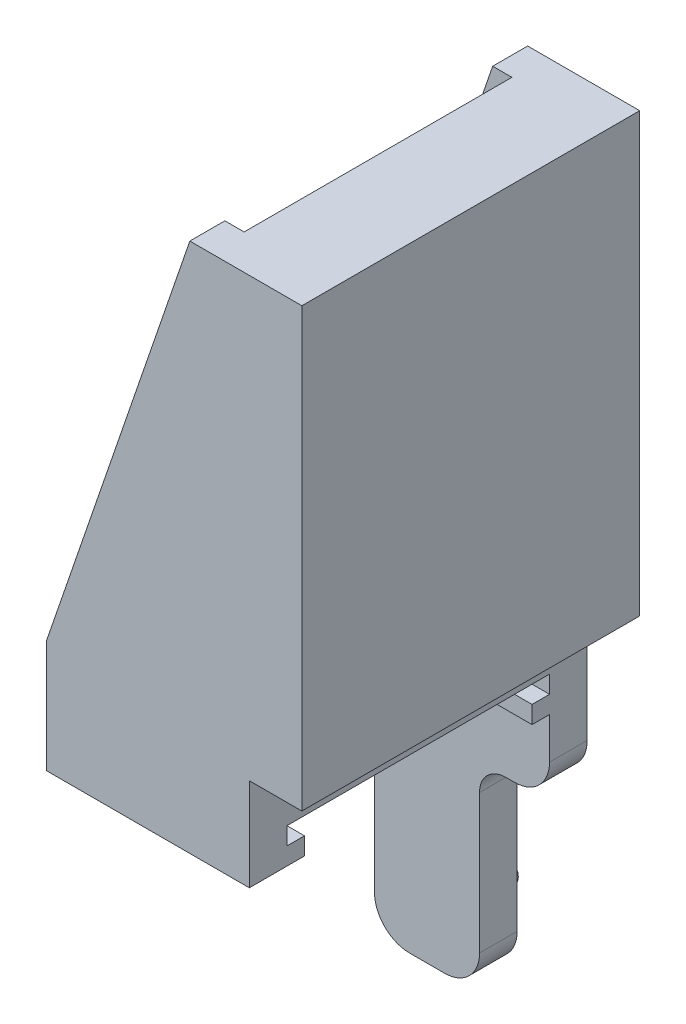
SolidWorks part; units mm, degrees
ref_plane "Alzado" through (0, 0, 0) normal (0, 0, 1) x (1, 0, 0)
ref_plane "Planta" through (0, 0, 0) normal (0, 1, 0) x (1, 0, 0)
ref_plane "Vista lateral" through (0, 0, 0) normal (1, 0, 0) x (0, 0, -1)
sketch "Croquis1" plane through (0, 0, 0) normal (0, 0, 1) x (1, 0, 0)
  line L0 (5.8, 23.05) -> (2.4, 23.05)
  line L2 (2.4, 23.05) -> (-5.8, -0.85)
  line L9 (1.8, -13.107) -> (1.8, -21.05)
  line L10 (-0.2, -23.05) -> (-2.2, -23.05)
  line L11 (-4.2, -21.05) -> (-4.2, -12.1093)
  line L12 (-4.7023, -11.6093) -> (-4.7953, -11.6097)
  line L13 (-5.8, -10.6097) -> (-5.8, -0.85)
  line L14 (3.3, -11.607) -> (3.8, -11.607)
  line L15 (5.8, -9.607) -> (5.8, 23.05)
  arc A0 (3.8, -11.607) -> (5.8, -9.607) centre (3.8, -9.607) ccw
  arc A1 (1.8, -13.107) -> (3.3, -11.607) centre (3.3, -13.107) cw
  arc A2 (1.8, -21.05) -> (-0.2, -23.05) centre (-0.2, -21.05) cw
  arc A3 (-2.2, -23.05) -> (-4.2, -21.05) centre (-2.2, -21.05) cw
  arc A4 (-4.7953, -11.6097) -> (-5.8, -10.6097) centre (-4.8, -10.6097) cw
  arc A5 (-4.2, -12.1093) -> (-4.7023, -11.6093) centre (-4.7, -12.1093) ccw
  point P0 (0, 0)
  dimension "D1" = 2
  dimension "D2" = 1.5
  dimension "D3" = 1
  dimension "D4" = 1.8
  dimension "D5" = 2.4
  dimension "D6" = 4.7023
  dimension "D7" = 4.7953
  dimension "D8" = 23.05
  dimension "D9" = 0.85
  dimension "D10" = 10.6097
  dimension "D11" = 11.607
  dimension "D12" = 23.05
extrude "Saliente-Extruir1" add sketch "Croquis1" along normal blind 19.3
sketch "Croquis2" plane through (-5.8, 0, 0) normal (-1, 0, 0) x (0, 0, 1)
  line L0 (0, -0.85) -> (0, -10.6097) construction
  line L1 (19.3, 23.05) -> (0, 23.05) construction
  line L2 (19.3, -10.6097) -> (0, -10.6097) construction
  line L3 (17.3, -3.25) -> (17.3, 23.05)
  line L4 (2, -3.25) -> (17.3, -3.25)
  line L5 (17.3, 23.05) -> (2, 23.05)
  line L6 (2, 23.05) -> (2, -3.25)
  dimension "D1" = 2
  dimension "D2" = 17.3
  dimension "D3" = 7.3597
extrude "Cortar-Extruir1" cut sketch "Croquis2" against normal blind 9.3 contours L3 L5 L6 L4
sketch "Croquis4" plane through (-5.8, 0, 0) normal (-1, 0, 0) x (0, 0, 1)
  line L0 (2.15, -5.25) -> (2.15, -6.25)
  line L1 (2.15, -23.25) -> (19.55, -23.25)
  line L2 (19.55, -23.25) -> (19.55, -7.25)
  line L3 (17.15, -5.25) -> (17.15, -6.25)
  line L4 (17.15, -6.25) -> (16.15, -6.25)
  line L5 (17.15, -5.25) -> (2.15, -5.25)
  line L10 (16.15, -6.25) -> (16.15, -7.25)
  line L11 (16.15, -7.25) -> (19.55, -7.25)
  line L12 (2.15, -6.25) -> (3.15, -6.25)
  line L13 (3.15, -6.25) -> (3.15, -7.25)
  line L14 (3.15, -7.25) -> (2.15, -7.25)
  line L15 (2.15, -7.25) -> (2.15, -23.25)
  line L18 (2, -3.25) -> (2, -0.85) construction
  line L19 (2, -0.85) -> (0, -0.85) construction
  dimension "D1" = 0.15
  dimension "D2" = 1.15
  dimension "D3" = 14.15
  dimension "D4" = 17.55
  dimension "D5" = 4.4
  dimension "D6" = 22.4
extrude "Cortar-Extruir2" cut sketch "Croquis4" against normal blind 12
sketch "Croquis5" plane through (0, 0, 0) normal (0, 0, -1) x (-1, 0, 0)
  circle A0 centre (0.8858, -20.3182) radius 0.75
extrude "Saliente-Extruir2" add sketch "Croquis5" along normal blind 2
sketch "Croquis6" plane through (5.8, 0, 0) normal (1, 0, 0) x (0, 0, -1)
  line L0 (0, -9.607) -> (0, 23.05) construction
  line L1 (-19.3, 23.05) -> (0, 23.05)
  line L2 (-19.3, 23.05) -> (-19.3, -1.95)
  line L3 (-19.3, -1.95) -> (0, -1.95)
  line L4 (0, 23.05) -> (0, -1.95)
  dimension "D1" = 25
extrude "Saliente-Extruir3" add sketch "Croquis6" along normal blind 3
